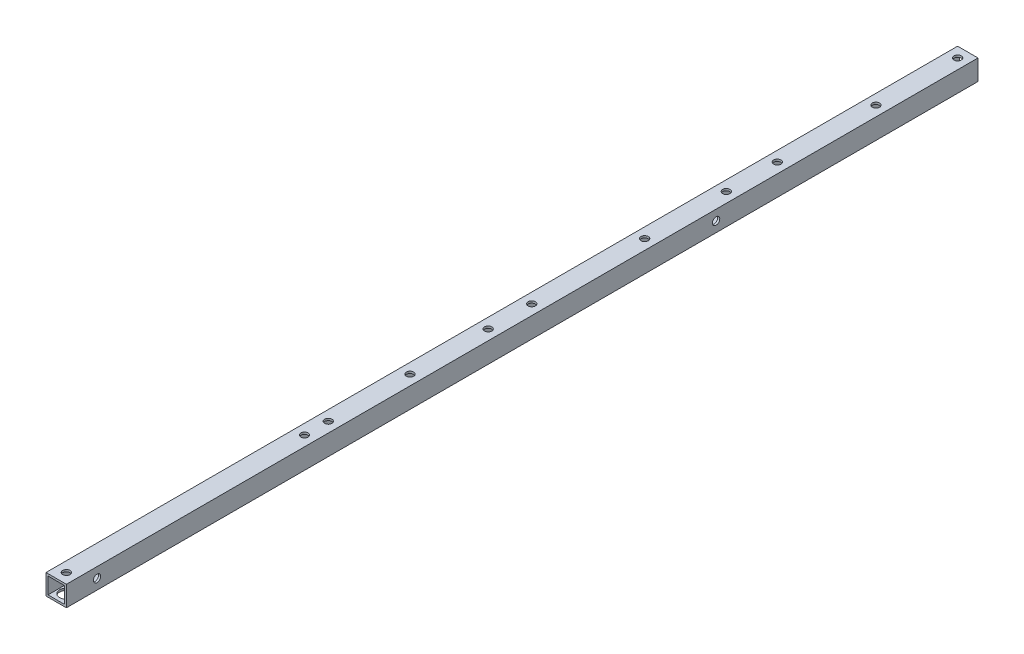
SolidWorks part; units mm, degrees
material "6063-T5"
ref_plane "正面" through (0, 0, 0) normal (0, 0, 1) x (1, 0, 0)
ref_plane "平面" through (0, 0, 0) normal (0, 1, 0) x (1, 0, 0)
ref_plane "右側面" through (0, 0, 0) normal (1, 0, 0) x (0, 0, -1)
sketch "ｽｹｯﾁ1" plane through (0, 0, 0) normal (0, 0, 1) x (1, 0, 0)
  line L1 (-7.5, -7.5) -> (7.5, -7.5)
  line L2 (-7.5, -7.5) -> (-7.5, 7.5)
  line L3 (-7.5, 7.5) -> (7.5, 7.5)
  line L4 (7.5, -7.5) -> (7.5, 7.5)
  line L5 (-7.5, -7.5) -> (7.5, 7.5) construction
  line L6 (-7.5, 7.5) -> (7.5, -7.5) construction
  line L7 (-6, -6) -> (6, -6)
  line L8 (-6, -6) -> (-6, 6)
  line L9 (-6, 6) -> (6, 6)
  line L10 (6, -6) -> (6, 6)
  line L11 (-6, -6) -> (6, 6) construction
  line L12 (-6, 6) -> (6, -6) construction
  point P0 (0, 0)
  point P6 (0, 0)
  dimension "D1" = 1.5
  dimension "D2" = 15
  dimension "D3" = 15
extrude "ﾎﾞｽ - 押し出し1" add sketch "ｽｹｯﾁ1" along normal blind 670
sketch "ｽｹｯﾁ4" plane through (7.5, 0, 0) normal (1, 0, 0) x (0, 0, -1)
  line L0 (-670, -7.5) -> (-670, 7.5) construction
  line L1 (-670, -7.5) -> (0, -7.5) construction
  circle A4 centre (-647.5, 0) radius 2.7
  circle A6 centre (-192.5, 0) radius 2.7
  dimension "D2" = 2
  dimension "D3" = 5.4
  dimension "D8" = 5.4
  dimension "D9" = 7.5
  dimension "D4" = 455
  dimension "D10" = 22.5
extrude "ｶｯﾄ - 押し出し3" cut sketch "ｽｹｯﾁ4" against normal blind 20
sketch "ｽｹｯﾁ3" plane through (0, 7.5, 0) normal (0, 1, 0) x (1, 0, 0)
  line L0 (7.5, -670) -> (-7.5, -670) construction
  line L1 (0, -662.5) -> (0, -177.5) construction
  line L2 (7.5, -670) -> (7.5, 0) construction
  circle A1 centre (0, -177.5) radius 2.7
  circle A6 centre (0, -487.5) radius 2.7
  circle A8 centre (0, -352.5) radius 2.7
  circle A9 centre (0, -662.5) radius 2.7
  circle A10 centre (0, -140) radius 2.7
  point P10 (0, -420)
  dimension "D2" = 492.5
  dimension "D3" = 5.4
  dimension "D7" = 135
  dimension "D8" = 7.5
  dimension "D9" = 7.5
  dimension "D11" = 5.4
  dimension "D4" = 7.5
  dimension "D5" = 5.4
  dimension "D12" = 67.5
  dimension "D10" = 7.5
  dimension "D13" = 37.5
  dimension "D6" = 2
extrude "ｶｯﾄ - 押し出し4" cut sketch "ｽｹｯﾁ3" against normal blind 30
sketch "ｽｹｯﾁ5" plane through (0, 7.5, 0) normal (0, 1, 0) x (1, 0, 0)
  line L0 (7.5, 0) -> (-7.5, 0) construction
  line L1 (7.5, -670) -> (7.5, 0) construction
  line L2 (7.5, -670) -> (-7.5, -670) construction
  circle A0 centre (0, -7.5) radius 2.7
  circle A1 centre (0, -67.5) radius 2.7
  circle A2 centre (0, -410) radius 2.7
  circle A3 centre (0, -470) radius 2.7
  dimension "D1" = 60
  dimension "D2" = 7.5
  dimension "D3" = 7.5
  dimension "D4" = 7.5
  dimension "D5" = 7.5
  dimension "D6" = 5.4
  dimension "D7" = 5.4
  dimension "D9" = 200
  dimension "D8" = 2
extrude "ｶｯﾄ - 押し出し5" cut sketch "ｽｹｯﾁ5" against normal blind 40
sketch "ｽｹｯﾁ6" plane through (0, -7.5, 0) normal (0, -1, 0) x (-1, 0, 0)
  circle A0 centre (0, -662.5) radius 5
  circle A1 centre (0, -177.5) radius 5
  circle A2 centre (0, -352.5) radius 5
  circle A3 centre (0, -487.5) radius 5
  circle A4 centre (0, -470) radius 5
  circle A5 centre (0, -410) radius 5
  circle A6 centre (0, -7.5) radius 5
  circle A7 centre (0, -67.5) radius 5
  circle A8 centre (0, -140) radius 5
  dimension "D1" = 10
  dimension "D2" = 10
  dimension "D3" = 10
  dimension "D4" = 10
  dimension "D5" = 10
  dimension "D6" = 10
  dimension "D7" = 2
extrude "ｶｯﾄ - 押し出し6" cut sketch "ｽｹｯﾁ6" against normal blind 10
sketch "ｽｹｯﾁ7" plane through (-7.5, 0, 0) normal (-1, 0, 0) x (0, 0, 1)
  circle A0 centre (192.5, 0) radius 5
  circle A1 centre (647.5, 0) radius 5
  dimension "D1" = 10
  dimension "D2" = 10
extrude "ｶｯﾄ - 押し出し7" cut sketch "ｽｹｯﾁ7" against normal blind 10
sketch "ｽｹｯﾁ8" plane through (0, 7.5, 0) normal (0, 1, 0) x (1, 0, 0)
  circle A0 centre (0, -177.5) radius 2.7 construction
  point P0 (0, -237.5)
  point P1 (0, -320.5)
  dimension "D2" = 60
  dimension "D1" = 83
hole_wizard "Ø5.4 (5.4) 直径の穴1" positions "ｽｹｯﾁ8" profile "ｽｹｯﾁ9" hole size "Ø5.4" standard "JIS" end condition through all
sketch "ｽｹｯﾁ9" plane through (0, 7.5, 237.5) normal (1, 0, 0) x (0, 0, 1)
  line L0 (0, 0) -> (0, 15)
  line L1 (0, 15) -> (2.7, 15)
  line L2 (2.7, 15) -> (2.7, 0)
  line L5 (2.7, 0) -> (0, 0)
  line L11 (0, -6.35) -> (0, 107.95) construction
  dimension "通し穴の直径" = 5.4
  dimension "通し穴の深さ" = 15
hole_wizard "Ø10.0 (10) 直径の穴1" positions "ｽｹｯﾁ10" profile "ｽｹｯﾁ12" hole size "Ø10.0" standard "JIS"
sketch "ｽｹｯﾁ10" plane through (0, -7.5, 0) normal (0, -1, 0) x (-1, 0, 0)
  point P0 (0, -237.5)
  point P3 (0, -320.5)
sketch "ｽｹｯﾁ12" plane through (0, -7.5, 237.5) normal (1, 0, 0) x (0, 0, -1)
  line L0 (0, 0) -> (0, 4.5043)
  line L1 (0, 4.5043) -> (5, 1.5)
  line L2 (5, 1.5) -> (5, 0)
  line L5 (5, 0) -> (0, 0)
  line L10 (0, 4.5043) -> (-5, 1.5) construction
  line L11 (0, -6.35) -> (0, 107.95) construction
  dimension "穴の直径" = 10
  dimension "穴の深さ" = 1.5
  dimension "ﾄﾞﾘﾙ角度" = 118
